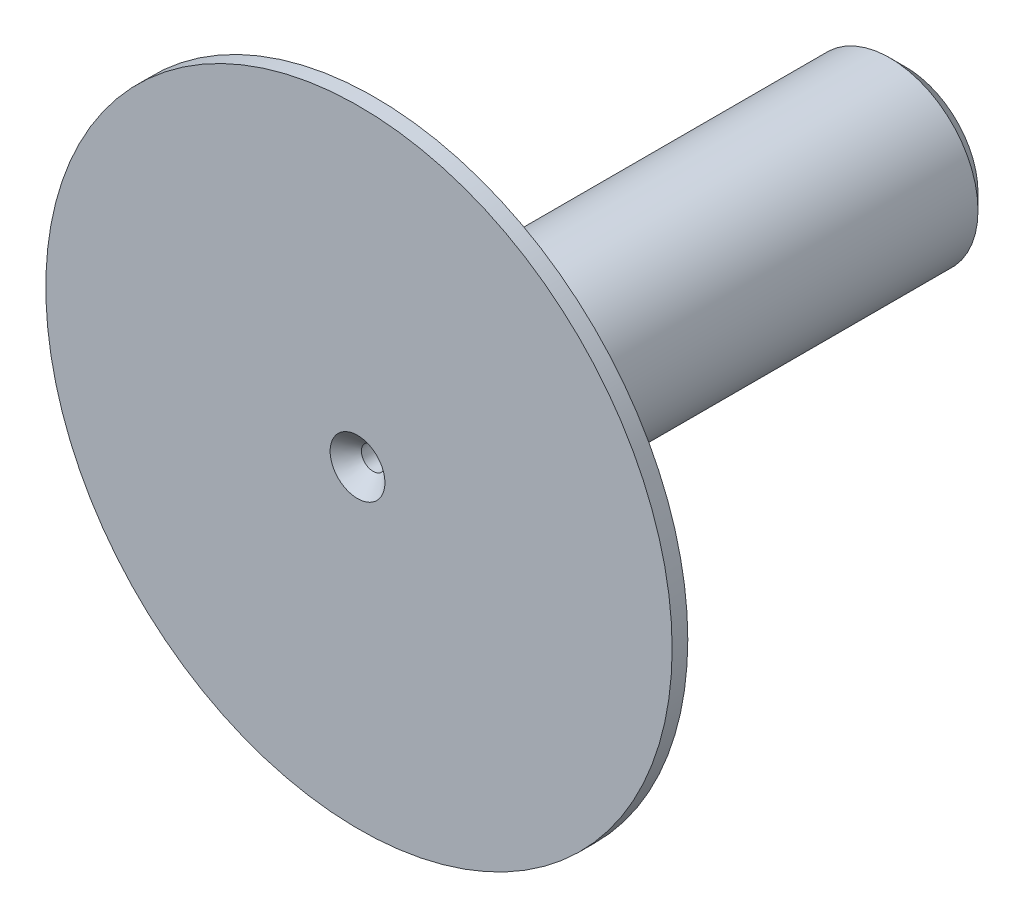
SolidWorks part; units mm, degrees
ref_plane "Front Plane" through (0, 0, 0) normal (0, 0, 1) x (1, 0, 0)
ref_plane "Top Plane" through (0, 0, 0) normal (0, 1, 0) x (1, 0, 0)
ref_plane "Right Plane" through (0, 0, 0) normal (1, 0, 0) x (0, 0, -1)
sketch "Sketch1" plane through (0, 0, 0) normal (0, 0, 1) x (1, 0, 0)
  circle A0 centre (0, 0) radius 0.15
  circle A1 centre (0, 0) radius 1.125
  dimension "D1" = 2.25
  dimension "D2" = 0.3
extrude "Boss-Extrude1" add sketch "Sketch1" along normal blind 7
sketch "Sketch2" plane through (0, 0, 7) normal (0, 0, 1) x (1, 0, 0)
  circle A0 centre (0, 0) radius 1.125
  circle A1 centre (0.0187, 0) radius 4
  circle A2 centre (0, 0) radius 1.125 construction
  dimension "D1" = 8
extrude "Boss-Extrude2" add sketch "Sketch2" against normal blind 0.2
chamfer "Chamfer1" distance 0.2 angle 45 3 edges at (1.125, 0, 0) (0.15, 0, 0) (0.15, 0, 7)
